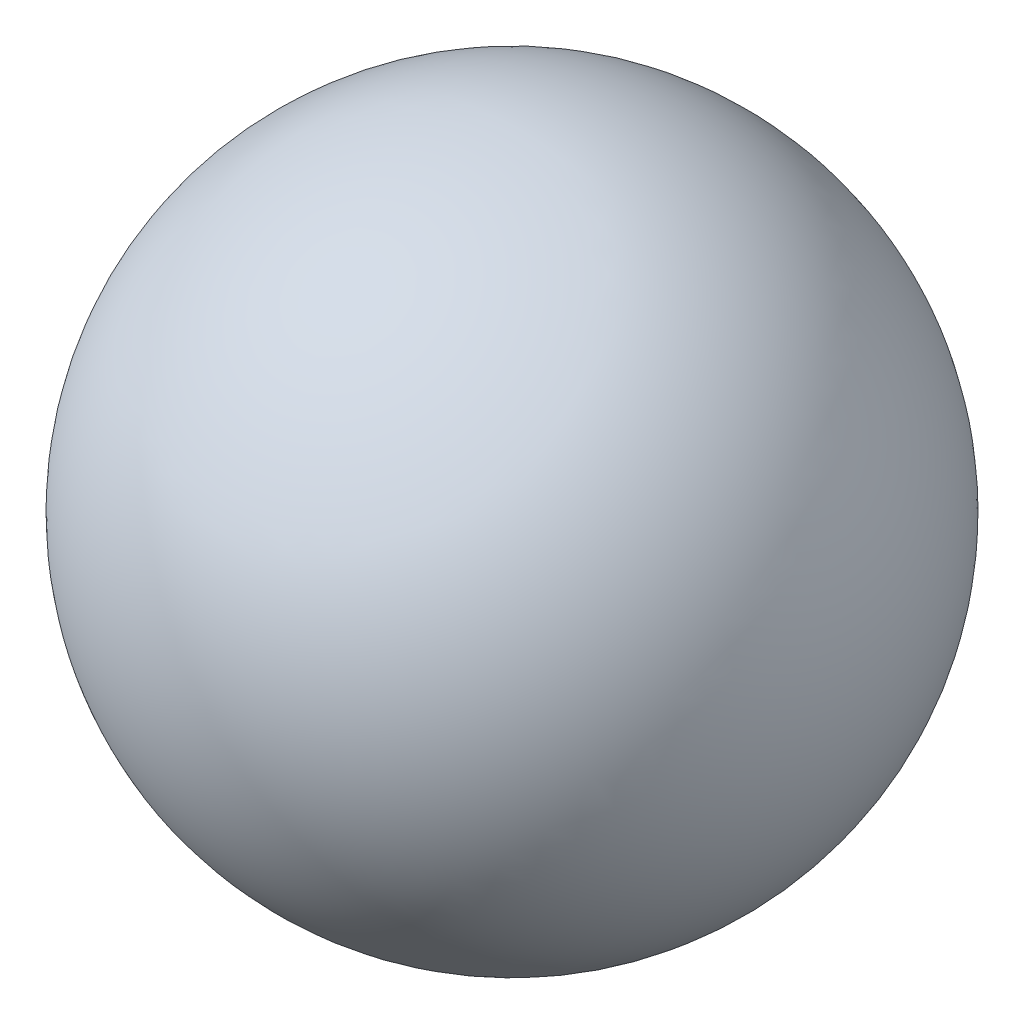
SolidWorks part; units mm, degrees
ref_plane "Front" through (0, 0, 0) normal (0, 0, 1) x (1, 0, 0)
ref_plane "Top" through (0, 0, 0) normal (0, 1, 0) x (1, 0, 0)
ref_plane "Right" through (0, 0, 0) normal (1, 0, 0) x (0, 0, -1)
sketch "Sketch2" plane through (0, 0, 0) normal (0, 0, 1) x (1, 0, 0)
  line L0 (0, 0) -> (0, 8) construction
  line L1 (0, 8) -> (0, 0)
  arc A0 (0, 8) -> (0, 0) centre (0, 4) cw
  dimension "D1" = 8
revolve "Revolve1" add sketch "Sketch2" angle 360 about L0
ref_plane "Plane1" through (0, 0, -4) normal (0, 0, -1) x (-1, 0, 0)
hole_wizard "M3x0.5 Tapped Hole1" positions "Sketch6" profile "Sketch7" tap size "M3x0.5" standard "ANSI Metric"
sketch "Sketch6" plane through (0, 0, -4) normal (0, 0, -1) x (-1, 0, 0)
  line L0 (0, 4) -> (0, 0) construction
  point P0 (0, 4)
  dimension "D1" = 4
sketch "Sketch7" plane through (0, 4, -4) normal (1, 0, 0) x (0, 1, 0)
  line L0 (0, 0) -> (0, 5.7511)
  line L1 (0, 5.7511) -> (1.25, 5)
  line L2 (1.25, 5) -> (1.25, 0.275)
  line L3 (1.25, 0.275) -> (1.525, 0)
  line L5 (1.525, 0) -> (0, 0)
  line L6 (-1.25, 0.275) -> (-1.525, 0) construction
  line L10 (0, 5.7511) -> (-1.25, 5) construction
  line L11 (0, -6.35) -> (0, 107.95) construction
  dimension "Tap Drill Dia." = 2.5
  dimension "Tap Drill Depth" = 5
  dimension "Near C'Sink Dia." = 3.05
  dimension "Near C'Sink Angle" = 90
  dimension "Drill Angle" = 118
cosmetic thread "Hole Thread1" parameters "D1"=5, "D2"=3
